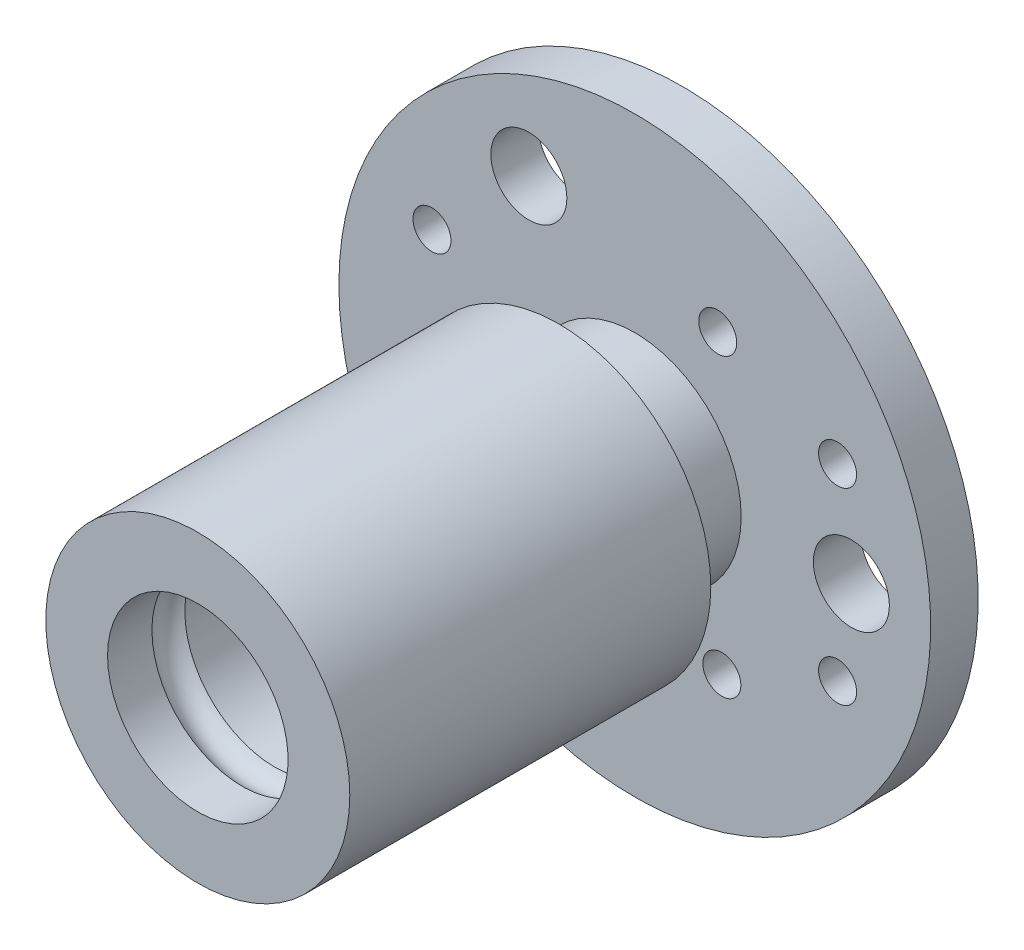
SolidWorks part; units mm, degrees
material "Alloy Steel"
ref_plane "Front Plane" through (0, 0, 0) normal (0, 0, 1) x (1, 0, 0)
ref_plane "Top Plane" through (0, 0, 0) normal (0, 1, 0) x (1, 0, 0)
ref_plane "Right Plane" through (0, 0, 0) normal (1, 0, 0) x (0, 0, -1)
sketch "Sketch1" plane through (0, 0, 0) normal (0, 0, 1) x (1, 0, 0)
  circle A0 centre (0, 0) radius 31.65
  dimension "D1" = 63.3
extrude "Boss-Extrude1" add sketch "Sketch1" along normal blind 5
chamfer "Chamfer1" distance 0.5 angle 45 2 edges at (31.65, 0, 0) (31.65, 0, 5)
sketch "Sketch2" plane through (0, 0, 5) normal (0, 0, 1) x (1, 0, 0)
  circle A0 centre (0, 0) radius 11.2
  dimension "D1" = 22.4
extrude "Boss-Extrude2" add sketch "Sketch2" along normal blind 8
sketch "Sketch3" plane through (0, 0, 13) normal (0, 0, 1) x (1, 0, 0)
  circle A0 centre (0, 0) radius 16
  circle A1 centre (0, 0) radius 11.2 construction
  dimension "D1" = 32
extrude "Boss-Extrude3" add sketch "Sketch3" along normal blind 38
sketch "Sketch5" plane through (0, 0, 0) normal (0, 0, -1) x (-1, 0, 0)
  circle A0 centre (0, 0) radius 9.5
  dimension "D1" = 19
extrude "Cut-Extrude2" cut sketch "Sketch5" against normal through all
sketch "Sketch6" plane through (0, 0, 0) normal (0, 0, -1) x (-1, 0, 0)
  line L2 (21.35, 8.0011) -> (21.35, 7.9)
  line L4 (-21.35, 8.0011) -> (-21.35, 7.9)
  line L23 (-21.35, -7.9) -> (-21.35, -8.0011)
  circle A0 centre (-21.35, 9.9) radius 2
  circle A1 centre (21.35, 9.9) radius 2
  circle A2 centre (-21.35, -9.9) radius 2
  circle A3 centre (21.35, -9.9) radius 2
  arc A4 (21.3875, 7.9004) -> (21.35, 8.0011) centre (0, 0) ccw
  circle A5 centre (-22.7982, -0.2876) radius 4
  circle A6 centre (11.15, 19.8876) radius 4
  circle A7 centre (11.6482, -19.6) radius 4
  circle A9 centre (-8.7325, 15.623) radius 2
  circle A10 centre (-9.1636, -15.374) radius 2
  circle A11 centre (17.8961, -0.2489) radius 2
  arc A16 (-21.35, 8.0011) -> (-21.3875, 7.9004) centre (0, 0) ccw
  arc A17 (-21.3875, -7.9004) -> (-21.35, -8.0011) centre (0, 0) ccw
  point P0 (0, 0)
  point P27 (0, 0)
  dimension "D3" = 3
  dimension "D8" = 31
  dimension "D9" = 22.8
  dimension "D1" = 42.7
  dimension "D2" = 19.8
extrude "Cut-Extrude3" cut sketch "Sketch6" against normal up to next
sketch "Sketch7" plane through (0, 0, 0) normal (0, 1, 0) x (1, 0, 0)
  line L0 (0, 0) -> (0, -44.6) construction
  line L1 (0, -44.6) -> (0, -48.7177) construction
  line L5 (-8.5, -42.6) -> (-8.5, -46.6)
  arc A0 (-8.5, -42.6) -> (-8.5, -46.6) centre (-8.5, -44.6) ccw
  dimension "D1" = 44.6
  dimension "D3" = 8.5
  dimension "D5" = 4
revolve "Cut-Revolve3" cut sketch "Sketch7" angle 360 about L1
ref_plane "Plane1" through (0, 0, 44.6) normal (0, 0, -1) x (-1, 0, 0)
sketch "Sketch8" plane through (0, 0, 0) normal (0, 0, -1) x (-1, 0, 0)
  circle A1 centre (0, 0) radius 31.15
  circle A2 centre (0, 0) radius 31.15
  circle A4 centre (-22.7982, -0.2876) radius 4
  circle A5 centre (11.15, 19.8876) radius 4
  point P13 (0, 0)
  dimension "D1" = 0
extrude "Cut-Extrude4" cut sketch "Sketch8" against normal blind 10 flip side to cut
